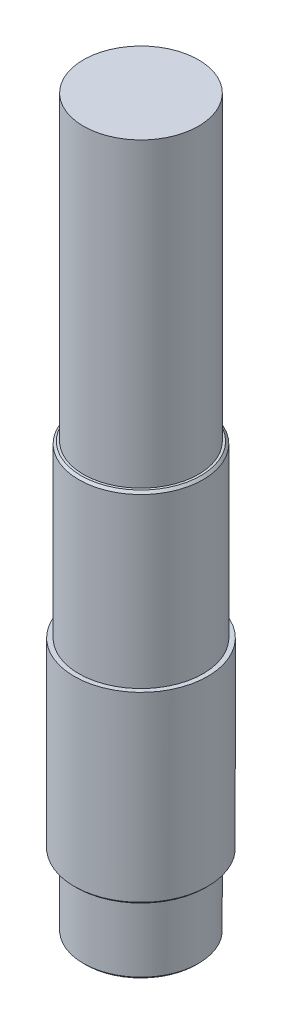
SolidWorks part; units mm, degrees
ref_plane "Front Plane" through (0, 0, 0) normal (0, 0, 1) x (1, 0, 0)
ref_plane "Top Plane" through (0, 0, 0) normal (0, 1, 0) x (1, 0, 0)
ref_plane "Right Plane" through (0, 0, 0) normal (1, 0, 0) x (0, 0, -1)
sketch "Sketch1" plane through (0, 0, 0) normal (0, 0, 1) x (1, 0, 0)
  line L0 (0, 87.3913) -> (0, -128.6087)
  line L1 (0, 87.3913) -> (-25, 87.3913)
  line L2 (-25, 87.3913) -> (-25, 56.3913)
  line L3 (-25, 56.3913) -> (-27, 56.3913)
  line L4 (-27, 56.3913) -> (-27, -17.6087)
  line L5 (-27, -17.6087) -> (-29, -17.6087)
  line L6 (-29, -17.6087) -> (-29, -97.6087)
  line L7 (-29, -97.6087) -> (-25, -97.6087)
  line L8 (-25, -97.6087) -> (-25, -128.6087)
  line L9 (-25, -128.6087) -> (0, -128.6087)
  dimension "D1" = 216
  dimension "D2" = 25
  dimension "D3" = 31
  dimension "D4" = 2
  dimension "D5" = 74
  dimension "D6" = 2
  dimension "D7" = 80
  dimension "D8" = 25
revolve "Revolve1" add sketch "Sketch1" angle 360 about L0
chamfer "Chamfer1" distance 1 angle 45 3 edges at (0, -97.6087, 29) (0, 56.3913, 27) (0, -128.6087, 25)
ref_plane "Plane1" through (-27, 0, 0) normal (-1, 0, 0) x (0, 0, 1)
sketch "Sketch2" plane through (-27, 0, 0) normal (-1, 0, 0) x (0, 0, 1)
  line L0 (0, -9.0883) -> (0, 38.9117) construction
  line L1 (-8, -9.0883) -> (-8, 38.9117)
  line L2 (8, -9.0883) -> (8, 38.9117)
  arc A0 (-8, -9.0883) -> (8, -9.0883) centre (0, -9.0883) ccw
  arc A1 (8, 38.9117) -> (-8, 38.9117) centre (0, 38.9117) ccw
  point P3 (0, 14.9117)
  dimension "D1" = 48
  dimension "D2" = 8
extrude "Cut-Extrude1" cut sketch "Sketch2" against normal blind 6
sketch "Sketch3" plane through (0, 87.3913, 0) normal (0, 1, 0) x (1, 0, 0)
  circle A0 centre (0, 0) radius 25
extrude "Boss-Extrude1" add sketch "Sketch3" along normal blind 100
